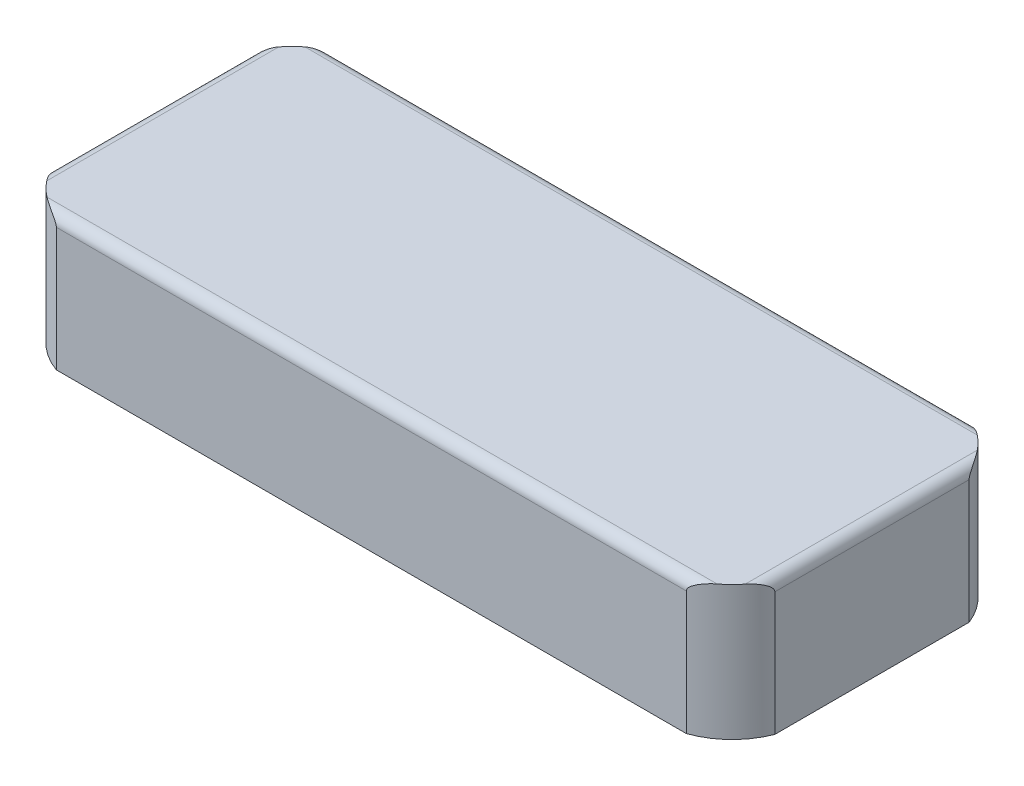
SolidWorks part; units mm, degrees
material "6061-T6 (SS)"
ref_plane "Front Plane" through (0, 0, 0) normal (0, 0, 1) x (1, 0, 0)
ref_plane "Top Plane" through (0, 0, 0) normal (0, 1, 0) x (1, 0, 0)
ref_plane "Right Plane" through (0, 0, 0) normal (1, 0, 0) x (0, 0, -1)
sketch "Sketch1" plane through (0, 0, 0) normal (0, 1, 0) x (1, 0, 0)
  line L1 (-215.9, -85.725) -> (215.9, -85.725)
  line L2 (-215.9, -85.725) -> (-215.9, 85.725)
  line L3 (-215.9, 85.725) -> (215.9, 85.725)
  line L4 (215.9, -85.725) -> (215.9, 85.725)
  line L5 (-215.9, -85.725) -> (215.9, 85.725) construction
  line L6 (-215.9, 85.725) -> (215.9, -85.725) construction
  point P0 (0, 0)
  dimension "D1" = 431.8
  dimension "D2" = 171.45
extrude "Boss-Extrude1" add sketch "Sketch1" along normal blind 85.725
sketch "Sketch2" plane through (0, 0, 0) normal (0, -1, 0) x (1, 0, 0)
  line L0 (-162.1689, -76.6864) -> (-162.1689, -85.725) construction
  line L1 (215.9, -85.725) -> (-215.9, -85.725) construction
  line L2 (-206.8614, -31.9939) -> (-215.9, -31.9939) construction
  line L3 (-215.9, -85.725) -> (-215.9, 85.725) construction
  line L4 (162.1689, -76.6864) -> (162.1689, -85.725) construction
  line L5 (206.8614, -31.9939) -> (215.9, -31.9939) construction
  line L6 (215.9, 85.725) -> (215.9, -85.725) construction
  line L7 (-162.1689, 76.6864) -> (-162.1689, 85.725) construction
  line L8 (-215.9, 85.725) -> (215.9, 85.725) construction
  line L9 (-206.8614, 31.9939) -> (-215.9, 31.9939) construction
  line L10 (206.8614, 31.9939) -> (215.9, 31.9939) construction
  line L11 (162.1689, 76.6864) -> (162.1689, 85.725)
  line L18 (162.1689, 76.6864) -> (-162.1689, 76.6864)
  line L19 (206.8614, -31.9939) -> (206.8614, 31.9939)
  line L20 (-162.1689, -76.6864) -> (162.1689, -76.6864)
  line L21 (-206.8614, 31.9939) -> (-206.8614, -31.9939)
  arc A0 (206.8614, -31.9939) -> (162.1689, -76.6864) centre (162.1689, -31.9939) cw
  arc A1 (162.1689, 76.6864) -> (206.8614, 31.9939) centre (162.1689, 31.9939) cw
  arc A2 (-162.1689, 76.6864) -> (-206.8614, 31.9939) centre (-162.1689, 31.9939) ccw
  arc A3 (-162.1689, -76.6864) -> (-206.8614, -31.9939) centre (-162.1689, -31.9939) cw
  dimension "D2" = 44.6926
extrude "Cut-Extrude1" cut sketch "Sketch2" against normal offset from surface (73.025 mm away) 12.7 contours A1 L19 A0 L20 A3 L21 A2 L18 up to face at (0, 85.725, 0)
fillet "Fillet3" radius 44.45 4 edges at (215.9, 42.8625, -85.725) (215.9, 42.8625, 85.725) (-215.9, 42.8625, 85.725) (-215.9, 42.8625, -85.725)
shell "Shell1" [suppressed] thickness 9.398
sketch "Sketch3" plane through (0, 85.725, 0) normal (0, 1, 0) x (1, 0, 0)
  line L0 (215.9, -41.275) -> (215.9, 41.275) construction
  line L1 (-171.45, -85.725) -> (171.45, -85.725) construction
  line L2 (-215.9, 41.275) -> (-215.9, -41.275) construction
  line L3 (171.45, 85.725) -> (-171.45, 85.725) construction
  line L4 (215.9, -41.275) -> (215.9, 41.275)
  line L5 (-171.45, -85.725) -> (171.45, -85.725)
  line L6 (-215.9, 41.275) -> (-215.9, -41.275)
  line L7 (171.45, 85.725) -> (-171.45, 85.725)
  arc A0 (215.9, 41.275) -> (171.45, 85.725) centre (171.45, 41.275) ccw construction
  arc A1 (171.45, -85.725) -> (215.9, -41.275) centre (171.45, -41.275) ccw construction
  arc A2 (-215.9, -41.275) -> (-171.45, -85.725) centre (-171.45, -41.275) ccw construction
  arc A3 (-171.45, 85.725) -> (-215.9, 41.275) centre (-171.45, 41.275) ccw construction
  arc A4 (215.9, 41.275) -> (171.45, 85.725) centre (171.45, 41.275) ccw
  arc A5 (171.45, -85.725) -> (215.9, -41.275) centre (171.45, -41.275) ccw
  arc A6 (-215.9, -41.275) -> (-171.45, -85.725) centre (-171.45, -41.275) ccw
  arc A7 (-171.45, 85.725) -> (-215.9, 41.275) centre (-171.45, 41.275) ccw
extrude "0.25 off the top" cut sketch "Sketch3" against normal blind 6.35
sketch "Sketch4" plane through (0, 0, 85.725) normal (0, 0, 1) x (1, 0, 0)
  line L1 (-215.9, 79.375) -> (215.9, 79.375)
  line L2 (-215.9, 79.375) -> (-215.9, 0)
  line L3 (-215.9, 0) -> (215.9, 0)
  line L4 (215.9, 79.375) -> (215.9, 0)
extrude "0.12 off the side" cut sketch "Sketch4" against normal blind 2.54
sketch "Sketch5" plane through (-215.9, 0, 0) normal (-1, 0, 0) x (0, 0, 1)
  line L1 (-85.725, 79.375) -> (83.185, 79.375)
  line L2 (-85.725, 79.375) -> (-85.725, 0)
  line L3 (-85.725, 0) -> (83.185, 0)
  line L4 (83.185, 79.375) -> (83.185, 0)
extrude "0.12 off the front" cut sketch "Sketch5" against normal blind 3.048
sketch "Sketch6" plane through (0, 0, -85.725) normal (0, 0, -1) x (-1, 0, 0)
  line L1 (-215.9, 79.375) -> (212.852, 79.375)
  line L2 (-215.9, 79.375) -> (-215.9, 0)
  line L3 (-215.9, 0) -> (212.852, 0)
  line L4 (212.852, 79.375) -> (212.852, 0)
extrude "Cut-Extrude5" cut sketch "Sketch6" against normal blind 3.048
sketch "Sketch7" plane through (215.9, 0, 0) normal (1, 0, 0) x (0, 0, -1)
  line L1 (-83.185, 79.375) -> (82.677, 79.375)
  line L2 (-83.185, 79.375) -> (-83.185, 0)
  line L3 (-83.185, 0) -> (82.677, 0)
  line L4 (82.677, 79.375) -> (82.677, 0)
extrude "Cut-Extrude6" cut sketch "Sketch7" against normal blind 3.048
sketch "Sketch8" plane through (0, 0, -82.677) normal (0, 0, -1) x (-1, 0, 0)
  line L0 (-255.5825, 19.05) -> (258.7675, 19.05)
  line L1 (-187.6264, 0) -> (187.6264, 0) construction
  dimension "D1" = 19.05
split line "Split Line1"
fillet "Fillet5" radius 6.35 4 edges at (212.852, 79.375, 0) (0, 79.375, -82.677) (-212.852, 79.375, 0) (0, 79.375, 83.185)
fillet "Fillet4" [suppressed] radius 0.762
equation "\"oring.277.ID\"= 11.484in"
equation "\"oring.277.A\"= 11.750in"
equation "\"oring.277.A1\"= 11.722in"
equation "\"oring.277.B\"= 11.500in"
equation "\"oring.277.B1\"= 11.528in"
equation "\"oring.277.C\"= 11.747in"
equation "\"oring.277.D\"= 11.503in"
equation "\"oring.277.G\"= 0.187in"
equation "\"D1@Sketch2\" = ( \"oring.279.A\" + \"anodize.add\" * 2 ) * PI"
equation "\"D2@Sketch2\"=12 * \"oring.279.W\" + ( \"oring.279.C.factor\" - \"oring.279.B1\" ) / 2"
equation "\"oring.277.W\"= 0.139in"
equation "\"anodize.add\"= 0.001in"
equation "\"c.factor\"= 0.00271"
equation "\"oring.277.C.factor\"= \"oring.277.C\" - \"oring.277.C\" * \"c.factor\""
equation "\"oring.279.ID\"= 12.984in"
equation "\"oring.279.A\"= 13.250in"
equation "\"oring.279.A1\"= 13.222in"
equation "\"oring.279.B\"= 13.000in"
equation "\"oring.279.B1\"= 13.028in"
equation "\"oring.279.C\"= 13.247in"
equation "\"oring.279.D\"= 13.003in"
equation "\"oring.279.G\"= 0.187in"
equation "\"oring.279.W\"= 0.139in"
equation "\"oring.279.C.factor\"= \"oring.279.C\" - \"oring.279.C\" * \"c.factor\""
